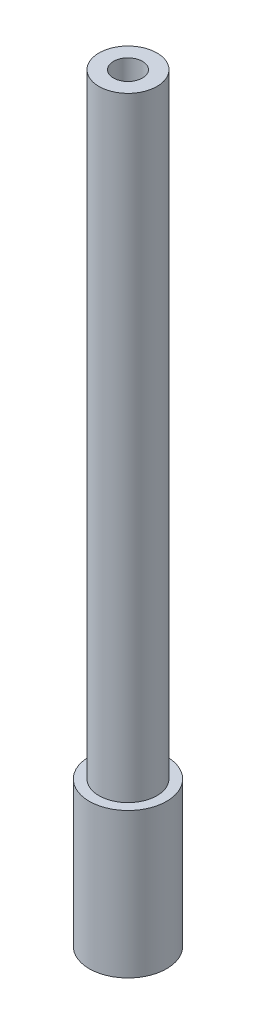
SolidWorks part; units mm, degrees
ref_plane "Front Plane" through (0, 0, 0) normal (0, 0, 1) x (1, 0, 0)
ref_plane "Top Plane" through (0, 0, 0) normal (0, 1, 0) x (1, 0, 0)
ref_plane "Right Plane" through (0, 0, 0) normal (1, 0, 0) x (0, 0, -1)
sketch "Sketch1" plane through (0, 0, 0) normal (0, 1, 0) x (1, 0, 0)
  circle A0 centre (0, 0) radius 4
  dimension "D1" = 8
extrude "Boss-Extrude1" add sketch "Sketch1" along normal blind 15
sketch "Sketch2" plane through (0, 15, 0) normal (0, 1, 0) x (1, 0, 0)
  circle A0 centre (0, 0) radius 3
  dimension "D1" = 6
extrude "Boss-Extrude2" add sketch "Sketch2" along normal blind 59.52
sketch "Sketch3" plane through (0, 0, 0) normal (0, -1, 0) x (1, 0, 0)
  circle A0 centre (0, 0) radius 1.02
  circle A1 centre (0, 0) radius 2.425
  dimension "D1" = 2.04
  dimension "D2" = 4.85
extrude "Cut-Extrude1" cut sketch "Sketch3" against normal blind 4
sketch "Sketch4" plane through (0, 74.52, 0) normal (0, 1, 0) x (1, 0, 0)
  circle A0 centre (0, 0) radius 3
extrude "Boss-Extrude3" add sketch "Sketch4" along normal blind 4
sketch "Sketch5" plane through (0, 78.52, 0) normal (0, 1, 0) x (1, 0, 0)
  circle A0 centre (0, 0) radius 1.5
  dimension "D1" = 3
extrude "Cut-Extrude2" cut sketch "Sketch5" against normal blind 50
